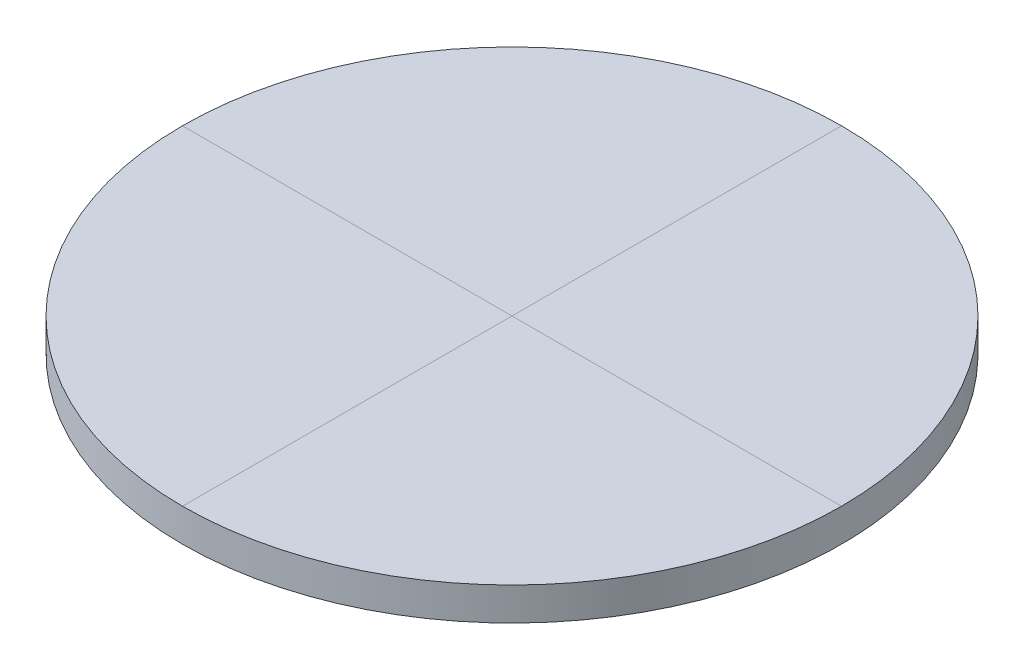
SolidWorks part; units mm, degrees
ref_plane "Front Plane" through (0, 0, 0) normal (0, 0, 1) x (1, 0, 0)
ref_plane "Top Plane" through (0, 0, 0) normal (0, 1, 0) x (1, 0, 0)
ref_plane "Right Plane" through (0, 0, 0) normal (1, 0, 0) x (0, 0, -1)
sketch "Sketch1" plane through (0, 0, 0) normal (0, 1, 0) x (1, 0, 0)
  circle A0 centre (0, 0) radius 30
  dimension "D1" = 60
extrude "Boss-Extrude1" add sketch "Sketch1" along normal blind 3
split line "Split Line1"
split line "Split Line2"
